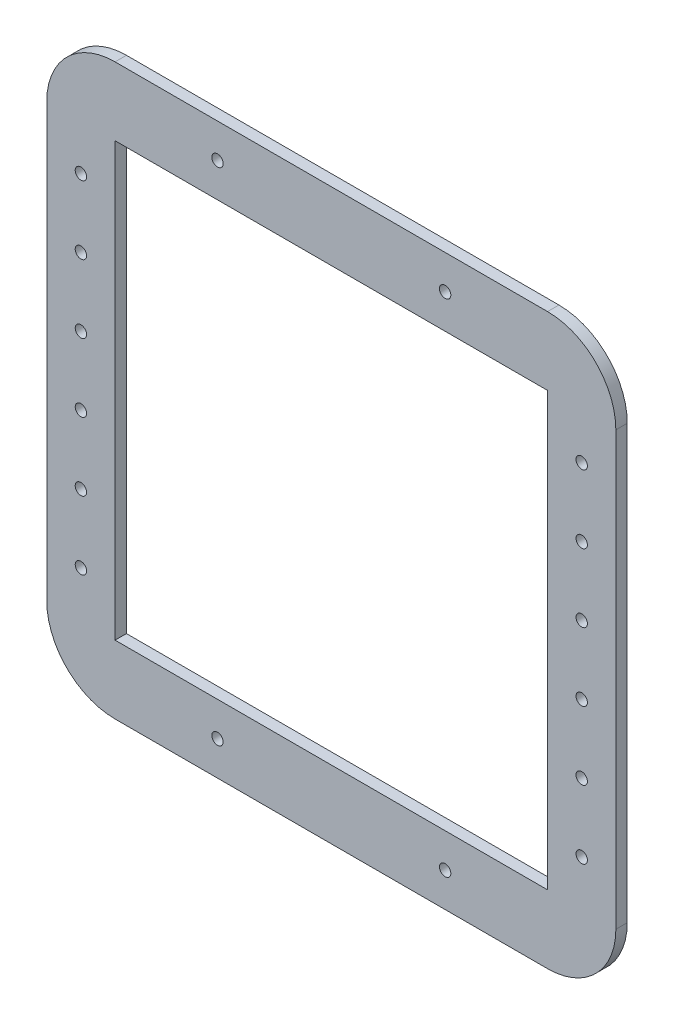
SolidWorks part; units mm, degrees
ref_plane "Front Plane" through (0, 0, 0) normal (0, 0, 1) x (1, 0, 0)
ref_plane "Top Plane" through (0, 0, 0) normal (0, 1, 0) x (1, 0, 0)
ref_plane "Right Plane" through (0, 0, 0) normal (1, 0, 0) x (0, 0, -1)
sketch "Sketch1" plane through (0, 0, 0) normal (0, 0, 1) x (1, 0, 0)
  line L0 (-95, 95) -> (-95, -95)
  line L1 (-95, 125) -> (95, 125)
  line L2 (-125, 95) -> (-125, -95)
  line L3 (-95, -125) -> (95, -125)
  line L4 (125, 95) -> (125, -95)
  line L5 (-125, 125) -> (125, -125) construction
  line L6 (-125, -125) -> (125, 125) construction
  line L7 (-95, -95) -> (95, -95)
  line L8 (95, 95) -> (95, -95)
  line L9 (-95, 95) -> (95, 95)
  arc A0 (-125, -95) -> (-95, -125) centre (-95, -95) ccw
  arc A1 (95, -125) -> (125, -95) centre (95, -95) ccw
  arc A2 (95, 125) -> (125, 95) centre (95, 95) cw
  arc A3 (-95, 125) -> (-125, 95) centre (-95, 95) ccw
  arc A4 (-95, -95) -> (-95, -95) centre (-95, -95) ccw
  arc A5 (95, -95) -> (95, -95) centre (95, -95) ccw
  arc A6 (95, 95) -> (95, 95) centre (95, 95) cw
  arc A7 (-95, 95) -> (-95, 95) centre (-95, 95) ccw
  point P0 (0, 0)
  dimension "D2" = 30
  dimension "D1" = 250
  dimension "D3" = 30
extrude "Boss-Extrude1" add sketch "Sketch1" along normal blind 5
sketch "Sketch2" plane through (0, 0, 5) normal (0, 0, 1) x (1, 0, 0)
  line L1 (-110, 75) -> (110, 75) construction
  line L2 (-110, 75) -> (-110, -75) construction
  line L3 (-110, -75) -> (110, -75) construction
  line L4 (110, 75) -> (110, -75) construction
  line L5 (-110, 75) -> (110, -75) construction
  line L6 (-110, -75) -> (110, 75) construction
  circle A0 centre (-110, 75) radius 2.5
  circle A1 centre (110, 75) radius 2.5
  point P0 (0, 0)
  dimension "D3" = 5
  dimension "D1" = 220
  dimension "D2" = 150
extrude "Cut-Extrude1" cut sketch "Sketch2" against normal through all
pattern_linear "LPattern1" count 6 spacing 30 along (0, -1, 0) of "Cut-Extrude1"
sketch "Sketch3" plane through (0, 0, 5) normal (0, 0, 1) x (1, 0, 0)
  line L0 (0, 0) -> (0, 95) construction
  line L1 (95, 95) -> (-95, 95) construction
  line L2 (-50, 125) -> (-50, 110) construction
  line L3 (95, 125) -> (-95, 125) construction
  line L4 (-50, 110) -> (-50, 95) construction
  line L5 (0, 0) -> (-95, 0) construction
  line L6 (-95, 95) -> (-95, -95) construction
  circle A1 centre (-50, 110) radius 2.5
  circle A2 centre (-110, 75) radius 2.5 construction
  circle A3 centre (50, 110) radius 2.5
  circle A4 centre (-50, -110) radius 2.5
  circle A5 centre (50, -110) radius 2.5
  dimension "D1" = 50
extrude "Cut-Extrude2" cut sketch "Sketch3" against normal through all
